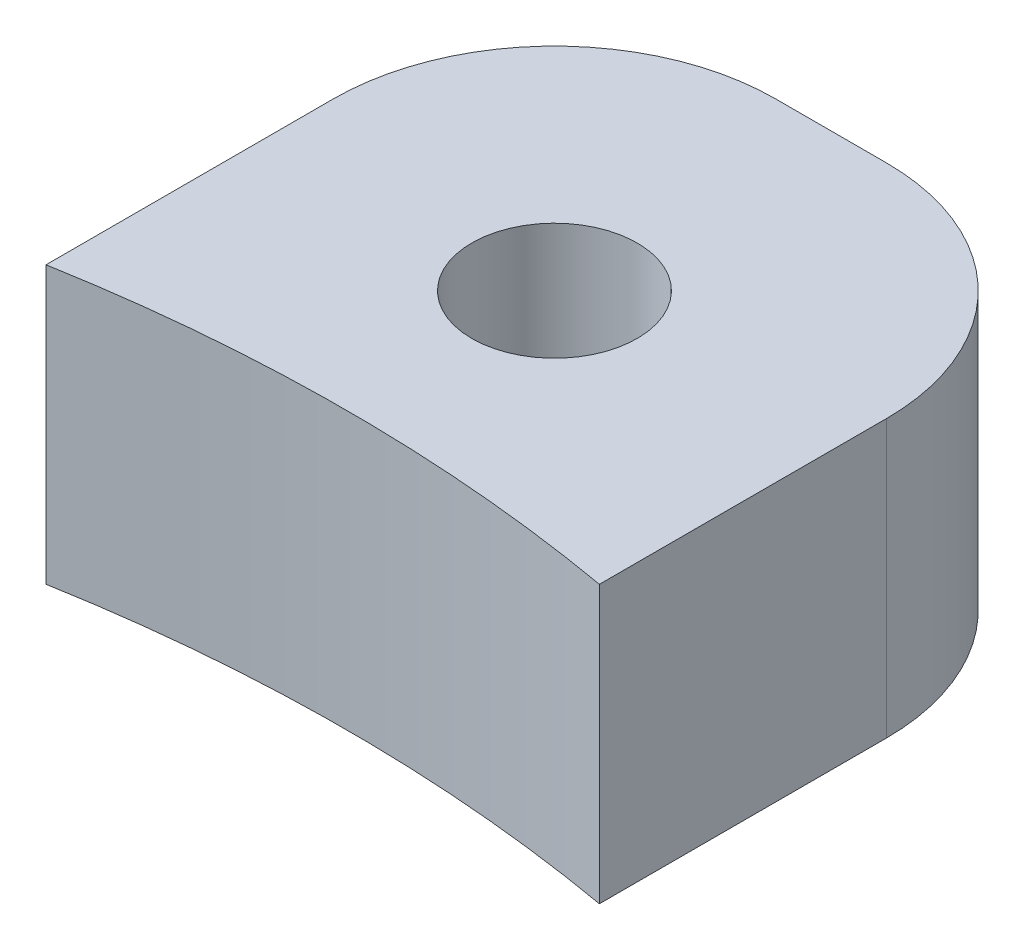
SolidWorks part; units mm, degrees
material "6061 Alloy"
ref_plane "Front Plane" through (0, 0, 0) normal (0, 0, 1) x (1, 0, 0)
ref_plane "Top Plane" through (0, 0, 0) normal (0, 1, 0) x (1, 0, 0)
ref_plane "Right Plane" through (0, 0, 0) normal (1, 0, 0) x (0, 0, -1)
sketch "Sketch1" plane through (0, 0, 0) normal (0, 1, 0) x (1, 0, 0)
  line L1 (-1.27, 22.225) -> (1.27, 22.225)
  line L2 (-6.35, 17.145) -> (-6.35, -25.4)
  line L3 (-6.35, -25.4) -> (6.35, -25.4)
  line L4 (6.35, 17.145) -> (6.35, -25.4)
  arc A0 (-1.27, 22.225) -> (-6.35, 17.145) centre (-1.27, 17.145) ccw
  arc A1 (6.35, 17.145) -> (1.27, 22.225) centre (1.27, 17.145) ccw
  point P7 (-6.35, 22.225)
  point P10 (6.35, 22.225)
  dimension "D5" = 5.08
  dimension "D1" = 12.7
  dimension "D2" = 47.625
  dimension "D3" = 25.4
  dimension "D4" = 6.35
extrude "Extrude1" add sketch "Sketch1" along normal blind 6.35
sketch "Sketch2" plane through (0, 6.35, 0) normal (0, 1, 0) x (-1, 0, 0)
  line L0 (6.35, 25.4) -> (-6.35, 25.4) construction
  circle A0 centre (0, 25.4) radius 36.5125
extrude "Cut-Extrude1" cut sketch "Sketch2" against normal blind 6.35
hole_wizard "#6 Clearance Hole1" positions "3DSketch1" profile "Sketch3" hole size "#6" standard "Ansi Inch"
sketch3d "3DSketch1"
  line L0 (6.35, 6.35, -10.5561) -> (6.35, 6.35, -17.145) construction
  line L1 (1.27, 6.35, -22.225) -> (-1.27, 6.35, -22.225) construction
  point P0 (0, 6.35, -15.875)
  dimension "D1" = 6.35
  dimension "D2" = 6.35
sketch "Sketch3" plane through (0, 6.35, -15.875) normal (1, 0, 0) x (0, 0, 1)
  line L0 (0, 0) -> (0, 331.3408)
  line L1 (0, 331.3408) -> (1.8986, 330.2)
  line L2 (1.8986, 330.2) -> (1.8986, 0)
  line L5 (1.8986, 0) -> (0, 0)
  line L10 (0, 331.3408) -> (-1.8987, 330.2) construction
  line L11 (0, -6.35) -> (0, 107.95) construction
  dimension "Hole Dia." = 3.7973
  dimension "Hole Depth" = 330.2
  dimension "Drill Angle" = 118
